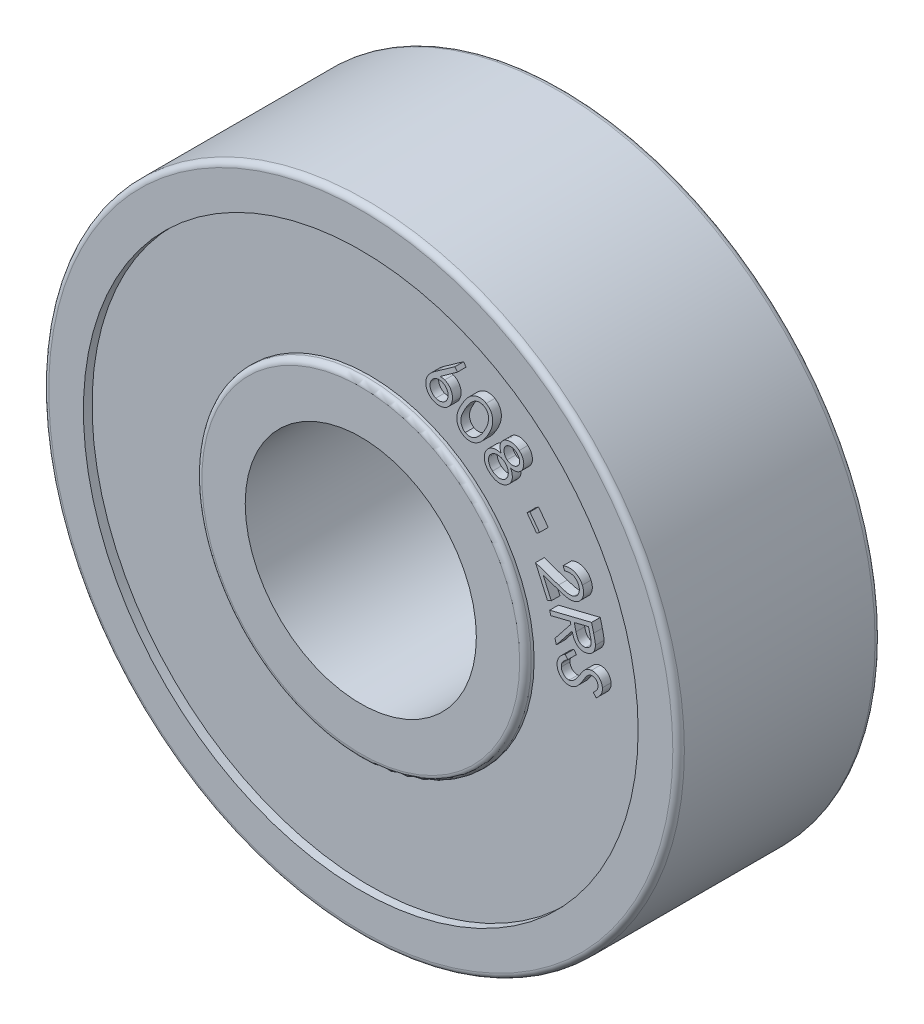
SolidWorks part; units mm, degrees
ref_plane "Front Plane" through (0, 0, 0) normal (0, 0, 1) x (1, 0, 0)
ref_plane "Top Plane" through (0, 0, 0) normal (0, 1, 0) x (1, 0, 0)
ref_plane "Right Plane" through (0, 0, 0) normal (1, 0, 0) x (0, 0, -1)
sketch "Sketch1" plane through (0, 0, 0) normal (0, 0, 1) x (1, 0, 0)
  circle A0 centre (0, 0) radius 4
  circle A1 centre (0, 0) radius 11
  dimension "D1" = 22
  dimension "D2" = 8
extrude "Boss-Extrude1" add sketch "Sketch1" along normal mid plane 7
sketch "Sketch2" plane through (0, 0, 3.5) normal (0, 0, 1) x (1, 0, 0)
  circle A0 centre (0, 0) radius 5.7
  circle A1 centre (0, 0) radius 9.6
  circle A2 centre (0, 0) radius 11 construction
  circle A3 centre (0, 0) radius 4 construction
  dimension "D1" = 1.4
  dimension "D2" = 1.7
extrude "Cut-Extrude1" cut sketch "Sketch2" against normal blind 0.3
mirror "Mirror1" about plane through (0, 0, 0) normal (0, 0, 1) of "Cut-Extrude1"
sketch "Sketch3" plane through (0, 0, 3.2) normal (0, 0, 1) x (1, 0, 0)
  circle A0 centre (0, 0) radius 6.875 construction
  text T0 "608 - 2RS\r\n" font "Century Gothic" height 1.5
  dimension "D1" = 13.75
extrude "Boss-Extrude2" add sketch "Sketch3" along normal blind 0.3
sketch "Sketch4" plane through (0, 0, -3.2) normal (0, 0, -1) x (-1, 0, 0)
  circle A0 centre (0, 0) radius 6.875 construction
  text T0 "608 - 2RS" font "Century Gothic" height 1.5
  dimension "D1" = 13.75
extrude "Boss-Extrude3" add sketch "Sketch4" along normal blind 0.3
fillet "Fillet1" radius 0.2 4 edges at (5.7, 0, 3.5) (5.7, 0, -3.5) (11, 0, 3.5) (11, 0, -3.5)
